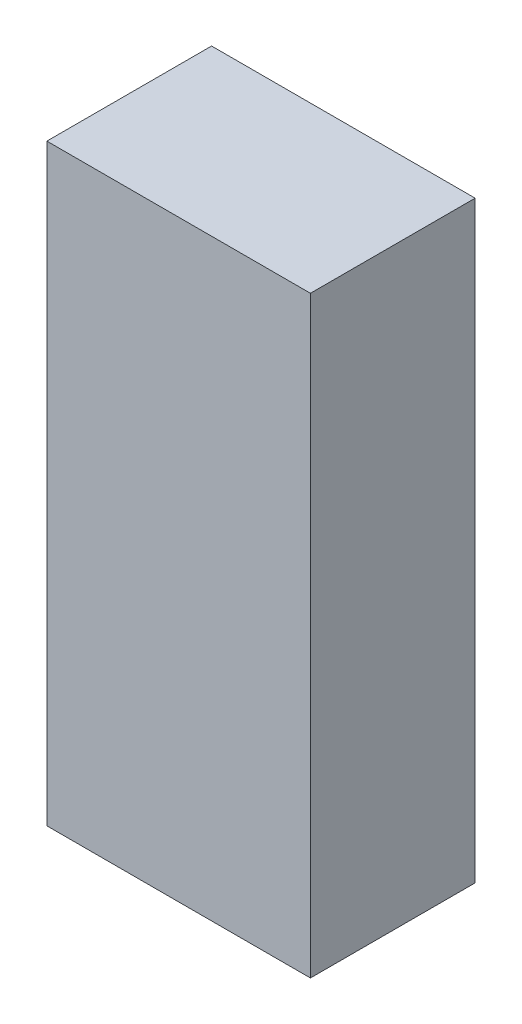
SolidWorks part; units mm, degrees
ref_plane "正面" through (0, 0, 0) normal (0, 0, 1) x (1, 0, 0)
ref_plane "平面" through (0, 0, 0) normal (0, 1, 0) x (1, 0, 0)
ref_plane "右側面" through (0, 0, 0) normal (1, 0, 0) x (0, 0, -1)
sketch "ｽｹｯﾁ1" plane through (0, 0, 0) normal (0, 0, 1) x (1, 0, 0)
  line L1 (-64.5409, 17.5406) -> (-32.5409, 17.5406)
  line L2 (-64.5409, 17.5406) -> (-64.5409, -54.4594)
  line L3 (-64.5409, -54.4594) -> (-32.5409, -54.4594)
  line L4 (-32.5409, 17.5406) -> (-32.5409, -54.4594)
  dimension "D1" = 72
  dimension "D2" = 32
extrude "ﾎﾞｽ - 押し出し1" add sketch "ｽｹｯﾁ1" along normal blind 20
